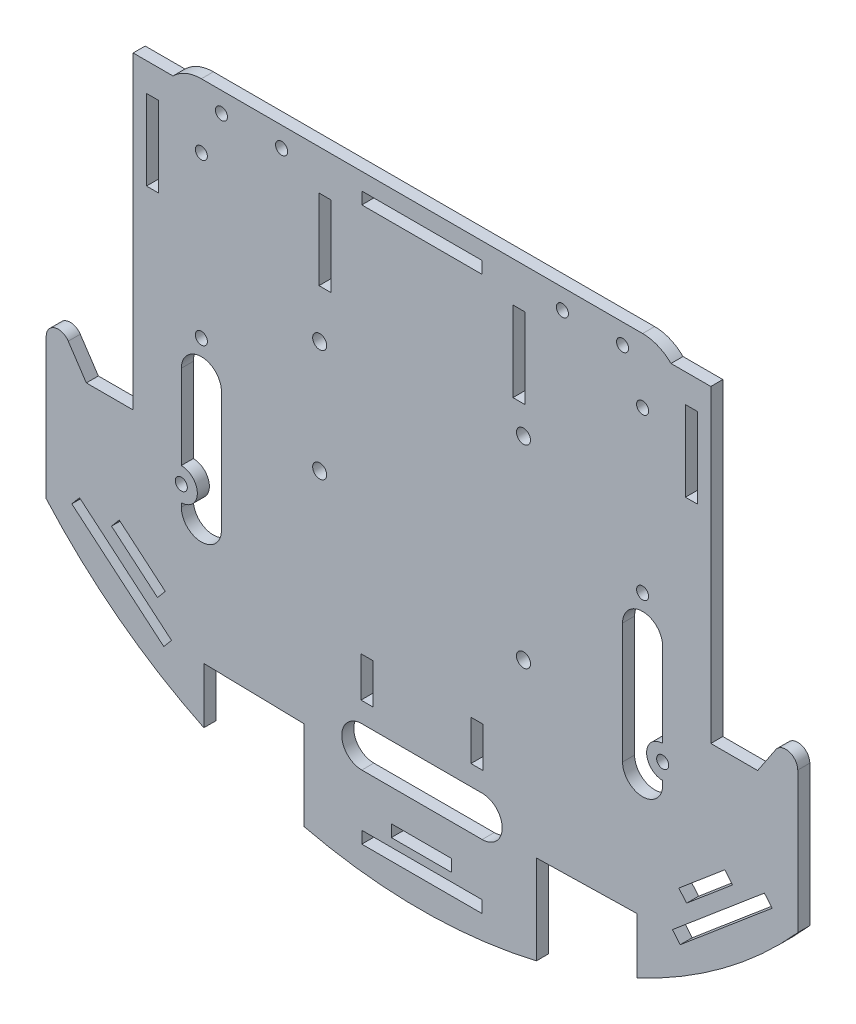
SolidWorks part; units mm, degrees
ref_plane "Front" through (0, 0, 0) normal (0, 0, 1) x (1, 0, 0)
ref_plane "Top" through (0, 0, 0) normal (0, 1, 0) x (1, 0, 0)
ref_plane "Right" through (0, 0, 0) normal (1, 0, 0) x (0, 0, -1)
sketch "Sketch1" plane through (0, 0, 0) normal (0, 0, 1) x (1, 0, 0)
  line L2 (-65, 40) -> (-65, -45)
  line L3 (-55, -55) -> (55, -55)
  line L4 (65, 40) -> (65, -45)
  line L5 (-55, 50) -> (55, 50)
  arc A0 (55, -55) -> (65, -45) centre (55, -45) ccw
  arc A1 (-65, -45) -> (-55, -55) centre (-55, -45) ccw
  arc A2 (55, 50) -> (65, 40) centre (55, 40) cw
  arc A3 (-65, 40) -> (-55, 50) centre (-55, 40) cw
  circle A4 centre (-50, 45) radius 1.5
  circle A5 centre (50, 45) radius 1.5
  circle A6 centre (-60, -40) radius 1.5
  circle A7 centre (60, -40) radius 1.5
  point P13 (60, -55)
  point P16 (65, 50)
  point P18 (60, 55)
  point P21 (-65, 50)
  dimension "D5" = 10
  dimension "D6" = 85
  dimension "D8" = 60
  dimension "D10" = 85
  dimension "D11" = 15
  dimension "D2" = 10
  dimension "D3" = 50
  dimension "D9" = 15
  dimension "D1" = 100
  dimension "D4" = 110
  dimension "D7" = 60
extrude "Boss-Extrude1" add sketch "Sketch1" along normal blind 3
sketch "Sketch3" plane through (0, 0, 0) normal (0, 0, -1) x (-1, 0, 0)
  line L0 (18.65, 45.2081) -> (-18.65, 45.2081) construction
  line L1 (0, 45.2081) -> (0, -45.2081) construction
  circle A0 centre (-18.65, 45.2081) radius 1.5
  circle A1 centre (18.65, 7.9081) radius 1.5
  circle A2 centre (-18.65, 7.9081) radius 1.5
  circle A3 centre (18.65, 45.2081) radius 1.5
  dimension "D1" = 37.3
  dimension "D2" = 37.3
  dimension "D3" = 37.3
  dimension "D4" = 37.3
sketch "Sketch5" plane through (0, 0, 0) normal (0, 0, -1) x (-1, 0, 0)
  line L0 (-37.465, 0.4556) -> (37.465, 0.4556) construction
  line L1 (0, 0.4556) -> (0, -0.4556) construction
  line L2 (-39.965, 0.4556) -> (-34.965, 0.4556) construction
  line L3 (-39.965, 1.9556) -> (-34.965, 1.9556)
  line L4 (-39.965, -1.0444) -> (-34.965, -1.0444)
  line L5 (-41.265, -47.8444) -> (-36.265, -47.8444) construction
  line L6 (-41.265, -46.3444) -> (-36.265, -46.3444)
  line L7 (-41.265, -49.3444) -> (-36.265, -49.3444)
  line L8 (34.965, 0.4556) -> (39.965, 0.4556) construction
  line L9 (34.965, 1.9556) -> (39.965, 1.9556)
  line L10 (34.965, -1.0444) -> (39.965, -1.0444)
  line L11 (41.465, -47.8444) -> (46.465, -47.8444) construction
  line L12 (41.465, -46.3444) -> (46.465, -46.3444)
  line L13 (41.465, -49.3444) -> (46.465, -49.3444)
  arc A6 (-39.965, 1.9556) -> (-39.965, -1.0444) centre (-39.965, 0.4556) ccw
  arc A7 (-34.965, -1.0444) -> (-34.965, 1.9556) centre (-34.965, 0.4556) ccw
  arc A8 (-41.265, -46.3444) -> (-41.265, -49.3444) centre (-41.265, -47.8444) ccw
  arc A9 (-36.265, -49.3444) -> (-36.265, -46.3444) centre (-36.265, -47.8444) ccw
  arc A10 (34.965, 1.9556) -> (34.965, -1.0444) centre (34.965, 0.4556) ccw
  arc A11 (39.965, -1.0444) -> (39.965, 1.9556) centre (39.965, 0.4556) ccw
  arc A12 (41.465, -46.3444) -> (41.465, -49.3444) centre (41.465, -47.8444) ccw
  arc A13 (46.465, -49.3444) -> (46.465, -46.3444) centre (46.465, -47.8444) ccw
  point P17 (-37.465, 0.4556)
  point P24 (-38.765, -47.8444)
  point P31 (37.465, 0.4556)
  point P38 (43.965, -47.8444)
  dimension "D2" = 1.3
  dimension "D3" = 74.93
  dimension "D4" = 48.3
  dimension "D5" = 6.5
  dimension "D9" = 3
  dimension "D10" = 5
sketch "Sketch7" plane through (0, 0, 0) normal (0, 0, -1) x (-1, 0, 0)
  line L0 (-34.25, -5.95) -> (-29.25, -5.95) construction
  line L1 (-37.4675, -25) -> (34.9684, -25) construction
  line L2 (0, -55) -> (0, -25) construction
  line L3 (55, -55) -> (-55, -55) construction
  line L4 (34.29, -51.67) -> (-34.29, -51.67) construction
  line L5 (34.29, -51.67) -> (34.29, 1.67) construction
  line L6 (34.29, 1.67) -> (-34.29, 1.67) construction
  line L7 (-34.29, -51.67) -> (-34.29, 1.67) construction
  line L8 (34.29, -51.67) -> (-34.29, 1.67) construction
  line L9 (34.29, 1.67) -> (-34.29, -51.67) construction
  line L10 (-34.25, -4.2) -> (-29.25, -4.2)
  line L11 (-34.25, -7.7) -> (-29.25, -7.7)
  line L12 (-34.25, -33.89) -> (-29.25, -33.89) construction
  line L13 (-34.25, -32.14) -> (-29.25, -32.14)
  line L14 (-34.25, -35.64) -> (-29.25, -35.64)
  line L15 (16.55, -49.13) -> (21.55, -49.13) construction
  line L16 (16.55, -47.38) -> (21.55, -47.38)
  line L17 (16.55, -50.88) -> (21.55, -50.88)
  line L18 (17.82, -0.87) -> (22.82, -0.87) construction
  line L19 (17.82, 0.88) -> (22.82, 0.88)
  line L20 (17.82, -2.62) -> (22.82, -2.62)
  arc A4 (-34.25, -4.2) -> (-34.25, -7.7) centre (-34.25, -5.95) ccw
  arc A5 (-29.25, -7.7) -> (-29.25, -4.2) centre (-29.25, -5.95) ccw
  arc A6 (-34.25, -32.14) -> (-34.25, -35.64) centre (-34.25, -33.89) ccw
  arc A7 (-29.25, -35.64) -> (-29.25, -32.14) centre (-29.25, -33.89) ccw
  arc A8 (16.55, -47.38) -> (16.55, -50.88) centre (16.55, -49.13) ccw
  arc A9 (21.55, -50.88) -> (21.55, -47.38) centre (21.55, -49.13) ccw
  arc A10 (17.82, 0.88) -> (17.82, -2.62) centre (17.82, -0.87) ccw
  arc A11 (22.82, -2.62) -> (22.82, 0.88) centre (22.82, -0.87) ccw
  point P21 (-31.75, -5.95)
  point P28 (-31.75, -33.89)
  point P35 (19.05, -49.13)
  point P42 (20.32, -0.87)
  dimension "D12" = 3.5
  dimension "D1" = 53.34
  dimension "D2" = 68.58
  dimension "D3" = 30
  dimension "D13" = 5
sketch "Sketch8" plane through (0, 0, 0) normal (0, 0, -1) x (-1, 0, 0)
  line L0 (34.29, -51.67) -> (34.29, 1.67)
  line L1 (34.29, 1.67) -> (-31.75, 1.67)
  line L2 (-34.29, -0.9648) -> (-34.29, -36.8539)
  line L3 (-34.29, -51.67) -> (-34.29, 1.67) construction
  line L4 (-34.29, -36.8539) -> (-31.75, -40.163)
  line L5 (-31.75, -40.163) -> (-31.75, -51.67)
  line L6 (34.29, -51.67) -> (-34.29, -51.67) construction
  line L7 (-31.75, -51.67) -> (34.29, -51.67)
  line L8 (-34.29, -0.9648) -> (-31.75, 1.67)
  dimension "D1" = 66.04
sketch "Sketch9" plane through (0, 0, 0) normal (0, 0, -1) x (-1, 0, 0)
  line L0 (30, -55) -> (30, -58)
  line L1 (55, -55) -> (-55, -55) construction
  line L2 (28, -60) -> (-28, -60)
  line L3 (-30, -58) -> (-30, -55)
  line L4 (-30, -55) -> (-15, -55)
  line L6 (15, -55) -> (15, -58)
  line L7 (-15, -55) -> (-15, -58)
  line L8 (15, -58) -> (-15, -58)
  line L9 (15, -55) -> (30, -55)
  arc A0 (-28, -60) -> (-30, -58) centre (-28, -58) cw
  arc A1 (30, -58) -> (28, -60) centre (28, -58) cw
  point P5 (0, -60)
  point P14 (-30, -60)
  point P17 (30, -60)
  dimension "D6" = 2
  dimension "D1" = 60
  dimension "D2" = 5
  dimension "D3" = 30
  dimension "D4" = 15
  dimension "D5" = 3
sketch "Sketch11" plane through (0, 0, 0) normal (0, 0, -1) x (-1, 0, 0)
  line L0 (-35, 10) -> (-35, 30) construction
  line L1 (-40, 10) -> (-40, 30)
  line L2 (-30, 10) -> (-30, 30)
  line L3 (0, 0) -> (0, 20) construction
  line L4 (35, 10) -> (35, 30) construction
  line L5 (30, 10) -> (30, 30)
  line L6 (40, 10) -> (40, 30)
  line L9 (-19.5, -7.5) -> (19.5, -7.5)
  line L10 (-22.5, -10.5) -> (-22.5, -39.5)
  line L11 (-19.5, -42.5) -> (19.5, -42.5)
  line L12 (22.5, -10.5) -> (22.5, -39.5)
  line L13 (-22.5, -7.5) -> (22.5, -42.5) construction
  line L14 (-22.5, -42.5) -> (22.5, -7.5) construction
  arc A0 (-40, 10) -> (-30, 10) centre (-35, 10) ccw
  arc A1 (-30, 30) -> (-40, 30) centre (-35, 30) ccw
  arc A2 (30, 10) -> (40, 10) centre (35, 10) ccw
  arc A3 (40, 30) -> (30, 30) centre (35, 30) ccw
  arc A4 (19.5, -7.5) -> (22.5, -10.5) centre (19.5, -10.5) cw
  arc A5 (19.5, -42.5) -> (22.5, -39.5) centre (19.5, -39.5) ccw
  arc A6 (-22.5, -39.5) -> (-19.5, -42.5) centre (-19.5, -39.5) ccw
  arc A7 (-19.5, -7.5) -> (-22.5, -10.5) centre (-19.5, -10.5) ccw
  point P2 (-35, 20)
  point P10 (0, -25)
  point P13 (35, 20)
  dimension "D7" = 3
  dimension "D11" = 20
  dimension "D3" = 5
  dimension "D13" = 5
  dimension "D2" = 20
  dimension "D4" = 45
  dimension "D5" = 35
  dimension "D6" = 25
  dimension "D8" = 20
sketch "Sketch12" plane through (0, 0, 0) normal (0, 0, -1) x (-1, 0, 0)
  line L0 (0, 0) -> (0, -20.7886) construction
  line L2 (65, 40) -> (65, -30)
  line L3 (65, -30) -> (72, -30)
  line L4 (72, 40) -> (72, -30)
  line L5 (65.675, 40) -> (68.675, 40)
  line L6 (65.675, 40) -> (65.675, 20)
  line L7 (65.675, 20) -> (68.675, 20)
  line L8 (68.675, 40) -> (68.675, 20)
  line L9 (-68.675, 40) -> (-68.675, 20)
  line L10 (-65.675, 20) -> (-68.675, 20)
  line L11 (-65.675, 40) -> (-65.675, 20)
  line L12 (-65.675, 40) -> (-68.675, 40)
  line L13 (-72, 40) -> (-72, -30)
  line L14 (-65, -30) -> (-72, -30)
  line L15 (-65, 40) -> (-65, -30)
  line L17 (62.0711, 47.0711) -> (72, 47.0711)
  line L18 (72, 47.0711) -> (72, 40)
  line L19 (-62.0711, 47.0711) -> (-72, 47.0711)
  line L20 (-72, 47.0711) -> (-72, 40)
  arc A0 (65, 40) -> (55, 50) centre (55, 40) ccw construction
  arc A1 (-55, 50) -> (-65, 40) centre (-55, 40) ccw construction
  arc A2 (-62.0711, 47.0711) -> (-65, 40) centre (-55, 40) ccw
  arc A3 (65, 40) -> (62.0711, 47.0711) centre (55, 40) ccw
  dimension "D1" = 70
  dimension "D2" = 7
  dimension "D3" = 0
extrude "Boss-Extrude3" add sketch "Sketch12" against normal blind 3
sketch "Sketch13" plane through (0, 0, 0) normal (0, 0, -1) x (-1, 0, 0)
  line L0 (65.675, 40) -> (65.675, 20) construction
  line L1 (25.675, 20) -> (22.675, 20)
  line L2 (25.675, 20) -> (25.675, 40)
  line L3 (25.675, 40) -> (22.675, 40)
  line L4 (22.675, 20) -> (22.675, 40)
  line L5 (0, 0) -> (0, -28.6176) construction
  line L6 (-22.675, 20) -> (-22.675, 40)
  line L7 (-25.675, 40) -> (-22.675, 40)
  line L8 (-25.675, 20) -> (-25.675, 40)
  line L9 (-25.675, 20) -> (-22.675, 20)
  line L11 (65.675, 20) -> (-50.335, 20) construction
  dimension "D1" = 3
  dimension "D2" = 40
  dimension "D3" = 20
  dimension "D4" = 0
extrude "Cut-Extrude5" cut sketch "Sketch13" against normal blind 3
sketch "Sketch14" plane through (0, 0, 0) normal (0, 0, -1) x (-1, 0, 0)
  line L0 (55, -30) -> (55, 0) construction
  line L1 (50, -30) -> (50, 0)
  line L2 (60, -30) -> (60, 0)
  line L3 (0, 0) -> (0, -9.2048) construction
  line L4 (-55, -30) -> (-55, 0) construction
  line L5 (-50, -30) -> (-50, 0)
  line L6 (-60, -30) -> (-60, 0)
  line L7 (65, -30) -> (65, -45) construction
  arc A0 (50, -30) -> (60, -30) centre (55, -30) ccw
  arc A1 (60, 0) -> (50, 0) centre (55, 0) ccw
  arc A2 (-50, -30) -> (-60, -30) centre (-55, -30) cw
  arc A3 (-60, 0) -> (-50, 0) centre (-55, 0) cw
  point P2 (55, -15)
  point P12 (-55, -15)
  dimension "D1" = 30
  dimension "D2" = 10
  dimension "D3" = 5
sketch "Sketch15" plane through (0, 0, 0) normal (0, 0, -1) x (-1, 0, 0)
  line L0 (72, 47.0711) -> (72, 47.5813)
  line L1 (-15, 42.7647) -> (-15, 39.7647)
  line L2 (-72, 47.5813) -> (-72, 47.0711)
  line L7 (-15, -95.2353) -> (15, -95.2353)
  line L8 (-15, -92.2353) -> (-15, -95.2353)
  line L9 (15, -92.2353) -> (-15, -92.2353)
  line L10 (15, -95.2353) -> (15, -92.2353)
  line L15 (55, 50) -> (-55, 50)
  line L16 (15, 39.7647) -> (15, 42.7647)
  line L17 (-15, 39.7647) -> (15, 39.7647)
  line L18 (15, 42.7647) -> (-15, 42.7647)
  line L20 (-65, -30) -> (-65, -45)
  line L21 (-55, -55) -> (55, -55)
  line L26 (65, -45) -> (65, -30)
  line L30 (55, 50) -> (-55, 50)
  line L34 (-65, -30) -> (-65, -45)
  line L35 (-55, -55) -> (55, -55)
  line L36 (-62.0711, 47.0711) -> (-72, 47.0711)
  line L37 (-62.0711, 47.0711) -> (-72, 47.0711)
  line L38 (-72, 47.0711) -> (-72, -30)
  line L39 (-72, 47.0711) -> (-72, -30)
  line L40 (65, -45) -> (65, -30)
  line L41 (-72, -30) -> (-65, -30)
  line L42 (54.3697, -77.9212) -> (54.3697, -89.8597)
  line L43 (-72, -30) -> (-65, -30)
  line L44 (55, 50) -> (-55, 50)
  line L45 (-73.675, -30) -> (-83.675, -30)
  line L46 (-83.675, -30) -> (-93.675, -15)
  line L47 (-93.675, -15) -> (-93.675, -60)
  line L48 (-43.5447, -77.9212) -> (-28.5447, -78.4478)
  line L49 (-28.5447, -78.4478) -> (-28.5447, -98.6579)
  line L50 (-43.5447, -77.9212) -> (-53.5447, -77.9212)
  line L51 (-53.5447, -77.9212) -> (-53.5447, -89.8597)
  line L52 (44.3697, -77.9212) -> (54.3697, -77.9212)
  line L53 (29.3697, -78.4478) -> (29.3697, -98.6579)
  line L54 (44.3697, -77.9212) -> (29.3697, -78.4478)
  line L63 (65, -30) -> (72, -30)
  line L64 (65, -30) -> (72, -30)
  line L65 (72, -30) -> (72, 47.0711)
  line L66 (72, 47.0711) -> (62.0711, 47.0711)
  line L67 (72, 47.0711) -> (62.0711, 47.0711)
  line L68 (93.675, -60) -> (93.675, -15)
  line L69 (93.675, -15) -> (83.675, -30)
  line L70 (83.675, -30) -> (73.675, -30)
  line L72 (87.2946, -57.9209) -> (85.3602, -55.6279)
  line L73 (64.3643, -77.2652) -> (87.2946, -57.9209)
  line L74 (62.4299, -74.9722) -> (64.3643, -77.2652)
  line L75 (85.3602, -55.6279) -> (62.4299, -74.9722)
  line L76 (-87.2946, -57.9209) -> (-64.3643, -77.2652)
  line L77 (-85.3602, -55.6279) -> (-87.2946, -57.9209)
  line L78 (-62.4299, -74.9722) -> (-85.3602, -55.6279)
  line L79 (-64.3643, -77.2652) -> (-62.4299, -74.9722)
  line L80 (65.9324, -67.4643) -> (77.394, -57.788)
  line L81 (63.9971, -65.172) -> (65.9324, -67.4643)
  line L82 (75.4588, -55.4957) -> (63.9971, -65.172)
  line L83 (77.394, -57.788) -> (75.4588, -55.4957)
  line L84 (-77.4228, -57.8227) -> (-65.9603, -67.4979)
  line L85 (-75.4878, -55.5302) -> (-77.4228, -57.8227)
  line L86 (-64.0252, -65.2054) -> (-75.4878, -55.5302)
  line L87 (-65.9603, -67.4979) -> (-64.0252, -65.2054)
  line L88 (-73.675, -30) -> (-72, -30)
  line L89 (73.675, -30) -> (72, -30)
  circle A0 centre (45, 40) radius 1.5
  circle A1 centre (-45, 40) radius 1.5
  circle A4 centre (-60, -40) radius 1.5
  circle A7 centre (60, -40) radius 1.5
  arc A9 (-93.675, -60) -> (-53.5447, -89.8597) centre (-0.4999, 23.3271) ccw
  arc A10 (-55, 50) -> (-62.0711, 47.0711) centre (-55, 40) ccw
  arc A11 (-65, -45) -> (-55, -55) centre (-55, -45) ccw
  arc A14 (55, -55) -> (65, -45) centre (55, -45) ccw
  arc A15 (62.0711, 47.0711) -> (55, 50) centre (55, 40) ccw
  arc A16 (-55, 50) -> (-62.0711, 47.0711) centre (-55, 40) ccw
  arc A17 (-65, -45) -> (-55, -55) centre (-55, -45) ccw
  arc A20 (55, -55) -> (65, -45) centre (55, -45) ccw
  arc A21 (62.0711, 47.0711) -> (55, 50) centre (55, 40) ccw
  arc A25 (-28.5447, -98.6579) -> (29.3697, -98.6579) centre (0.4125, 22.9417) ccw
  arc A29 (54.3697, -89.7916) -> (93.675, -60) centre (0, 22.7647) ccw
  dimension "D14" = 125
  dimension "D2" = 0
  dimension "D3" = 3
  dimension "D4" = 3
  dimension "D5" = 3
  dimension "D8" = 27.6999
  dimension "D9" = 21.2175
  dimension "D10" = 21.2618
  dimension "D11" = 27.6999
  dimension "D15" = 15
  dimension "D16" = 10
extrude "Boss-Extrude4" add sketch "Sketch15" against normal blind 3
sketch "Sketch16" plane through (0, 0, 0) normal (0, 0, -1) x (-1, 0, 0)
  line L0 (-60, -44) -> (-60, -45)
  line L1 (60, -36) -> (60, -15)
  line L52 (50, -15) -> (50, -45)
  line L53 (60, -45) -> (60, -44)
  line L56 (-50, -45) -> (-50, -15)
  line L57 (-60, -15) -> (-60, -36)
  arc A0 (60, -36) -> (60, -44) centre (60, -40) ccw
  arc A1 (-60, -44) -> (-60, -36) centre (-60, -40) ccw
  arc A60 (60, -15) -> (50, -15) centre (55, -15) ccw
  arc A61 (50, -45) -> (60, -45) centre (55, -45) ccw
  arc A64 (-50, -15) -> (-60, -15) centre (-55, -15) ccw
  arc A65 (-60, -45) -> (-50, -45) centre (-55, -45) ccw
  dimension "D1" = 8
  dimension "D2" = 8
extrude "Cut-Extrude7" cut sketch "Sketch16" against normal blind 3
sketch "Sketch17" plane through (0, 0, 0) normal (0, 0, -1) x (-1, 0, 0)
  line L0 (-15, -74.2353) -> (15, -74.2353) construction
  line L1 (-15, -69.2353) -> (15, -69.2353)
  line L2 (-15, -79.2353) -> (15, -79.2353)
  line L7 (15, -92.2353) -> (-15, -92.2353) construction
  arc A0 (-15, -69.2353) -> (-15, -79.2353) centre (-15, -74.2353) ccw
  arc A1 (15, -79.2353) -> (15, -69.2353) centre (15, -74.2353) ccw
  point P2 (0, -74.2353)
  dimension "D2" = 5
  dimension "D1" = 18
  dimension "D3" = 30
extrude "Cut-Extrude8" cut sketch "Sketch17" against normal blind 5
sketch "Sketch18" plane through (0, 0, 0) normal (0, 0, -1) x (-1, 0, 0)
  line L0 (-55, 50) -> (55, 50) construction
  line L2 (-15, 45.7647) -> (15, 45.7647)
  line L3 (-15, 45.7647) -> (-15, 42.7647)
  line L4 (-15, 42.7647) -> (15, 42.7647)
  line L5 (-55, -6) -> (55, 34) construction
  line L6 (-55, 34) -> (55, -6) construction
  line L7 (15, 45.7647) -> (15, 42.7647)
  line L8 (15, -92.2353) -> (-15, -92.2353) construction
  circle A0 centre (55, 34) radius 1.5
  circle A1 centre (55, -6) radius 1.5
  circle A2 centre (-55, 34) radius 1.5
  circle A3 centre (-55, -6) radius 1.5
  point P0 (0, 14)
  dimension "D3" = 16
  dimension "D4" = 16
  dimension "D1" = 110
  dimension "D2" = 40
  dimension "D5" = 135
extrude "Cut-Extrude9" cut sketch "Sketch18" against normal blind 3
sketch "Sketch24" plane through (0, 0, 3) normal (0, 0, 1) x (1, 0, 0)
  circle A0 centre (-55, 34) radius 4
  circle A1 centre (55, 34) radius 4
  dimension "D1" = 8
  dimension "D2" = 8
fillet "Fillet4" radius 3 2 edges at (93.675, -15, 1.5) (-93.675, -15, 1.5)
sketch "Sketch25" plane through (0, 0, 3) normal (0, 0, 1) x (1, 0, 0)
  line L0 (0, 50) -> (0, 47.2574) construction
  line L1 (55, 50) -> (-55, 50) construction
  circle A0 centre (-35, 45) radius 1.5
  circle A1 centre (35, 45) radius 1.5
  dimension "D1" = 3
  dimension "D2" = 5
  dimension "D3" = 35
extrude "Cut-Extrude11" cut sketch "Sketch25" against normal blind 10
sketch "Sketch26" plane through (0, 0, 3) normal (0, 0, 1) x (1, 0, 0)
  line L0 (-54.3697, -77.9212) -> (-54.3697, -75.9212)
  line L2 (-54.3697, -77.9212) -> (-29.3697, -78.4478)
  line L3 (-29.3697, -78.4478) -> (-29.3697, -76.4508)
  line L4 (-29.3697, -76.4508) -> (-54.3697, -75.9212)
  line L6 (28.5447, -78.4478) -> (28.5447, -76.4508)
  line L7 (53.5447, -77.9212) -> (28.5447, -78.4478)
  line L8 (53.5447, -77.9212) -> (53.5447, -75.9212)
  line L9 (28.5447, -76.4508) -> (53.5447, -75.9212)
  dimension "D1" = 2
  dimension "D2" = 1.9969
extrude "Cut-Extrude12" cut sketch "Sketch26" against normal blind 10
sketch "Sketch27" plane through (0, 0, 0) normal (0, 0, -1) x (-1, 0, 0)
  line L0 (0, -79.2353) -> (0, -102.0576) construction
  line L2 (15, -92.2353) -> (-15, -92.2353) construction
  line L3 (-7.352, -90.1453) -> (7.648, -90.1453)
  line L4 (-7.352, -90.1453) -> (-7.352, -87.1453)
  line L5 (-7.352, -87.1453) -> (7.648, -87.1453)
  line L6 (7.648, -90.1453) -> (7.648, -87.1453)
  line L7 (-15, -79.2353) -> (15, -79.2353) construction
  arc A1 (-28.5447, -98.6579) -> (29.3697, -98.6579) centre (0.4125, 22.9417) ccw construction
  dimension "D1" = 2.09
  dimension "D2" = 3
  dimension "D3" = 7.352
  dimension "15" = 15
extrude "Cut-Extrude13" cut sketch "Sketch27" against normal blind 10
sketch "Sketch34" plane through (0, 0, 3) normal (0, 0, 1) x (1, 0, 0)
  line L0 (0, -69.2353) -> (0, -37.9332) construction
  line L1 (-15, -69.2353) -> (15, -69.2353) construction
  line L2 (12.2, -54.2353) -> (15.2, -54.2353)
  line L7 (15.2, -64.2353) -> (15.2, -54.2353)
  line L8 (12.2, -64.2353) -> (15.2, -64.2353)
  line L9 (-12.2, -64.2353) -> (-15.2, -64.2353)
  line L10 (-12.2, -64.2353) -> (-12.2, -54.2353)
  line L11 (-12.2, -54.2353) -> (-15.2, -54.2353)
  line L12 (-15.2, -64.2353) -> (-15.2, -54.2353)
  line L13 (-12.2, -64.2353) -> (-15.2, -54.2353) construction
  line L14 (-12.2, -54.2353) -> (-15.2, -64.2353) construction
  line L15 (12.2, -64.2353) -> (12.2, -54.2353)
  point P5 (17.3521, -60.9771)
  point P10 (-13.7, -59.2353)
  dimension "D1" = 1.5
  dimension "D2" = 10
  dimension "D3" = 13.7
  dimension "D4" = 5
extrude "Cut-Extrude14" cut sketch "Sketch34" against normal blind 10
sketch "Sketch35" plane through (0, 0, 3) normal (0, 0, 1) x (1, 0, 0)
  line L1 (55, 50) -> (-55, 50) construction
  line L2 (0, 0) -> (0, 50) construction
  circle A0 centre (25.3, -35.3) radius 1.75
  circle A1 centre (-25.5, -19.9) radius 1.75
  circle A2 centre (25.3, 13) radius 1.75
  circle A3 centre (-25.5, 8) radius 1.75
  point P8 (0, 0)
  point P9 (0, 0)
  point P12 (92.9711, -52.0466)
  point P15 (-27.7527, 6.7412)
  dimension "D1" = 3.5
  dimension "D2" = 3.5
  dimension "D3" = 3.5
  dimension "D4" = 3.5
  dimension "D5" = 48.3
  dimension "D6" = 50.8
  dimension "D7" = 27.9
  dimension "D8" = 50.8
  dimension "D9" = 5
  dimension "D10" = 37
  dimension "D11" = 25.5
extrude "Cut-Extrude15" cut sketch "Sketch35" against normal blind 10
